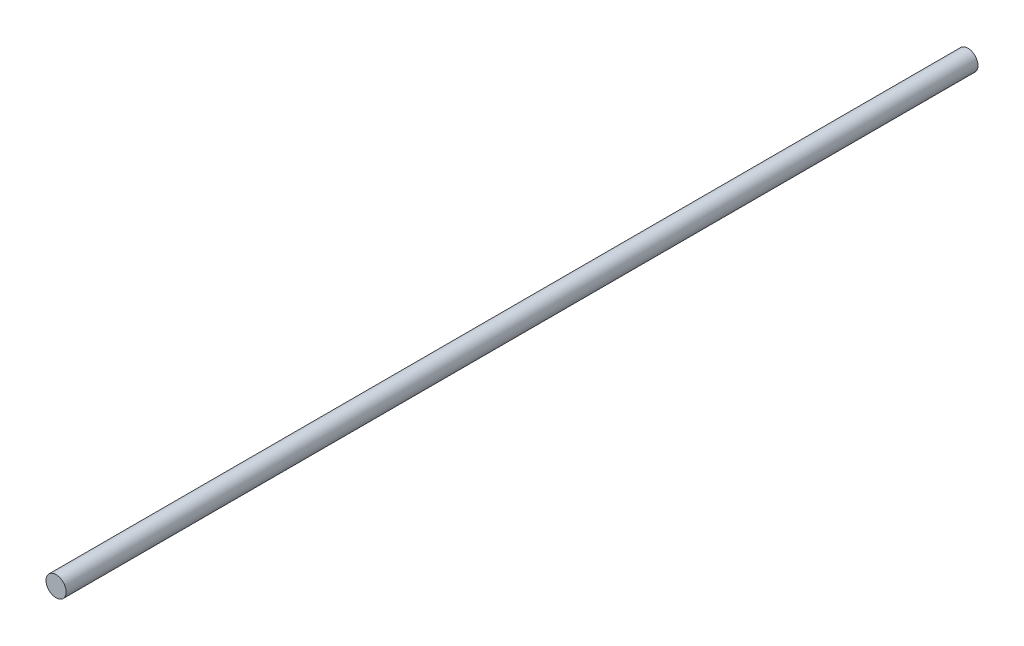
SolidWorks part; units mm, degrees
ref_plane "前视基准面" through (0, 0, 0) normal (0, 0, 1) x (1, 0, 0)
ref_plane "上视基准面" through (0, 0, 0) normal (0, 1, 0) x (1, 0, 0)
ref_plane "右视基准面" through (0, 0, 0) normal (1, 0, 0) x (0, 0, -1)
sketch "草图1" plane through (0, 0, 0) normal (0, 0, 1) x (1, 0, 0)
  circle A0 centre (0, 0) radius 4
extrude "凸台-拉伸1" add sketch "草图1" along normal blind 362
